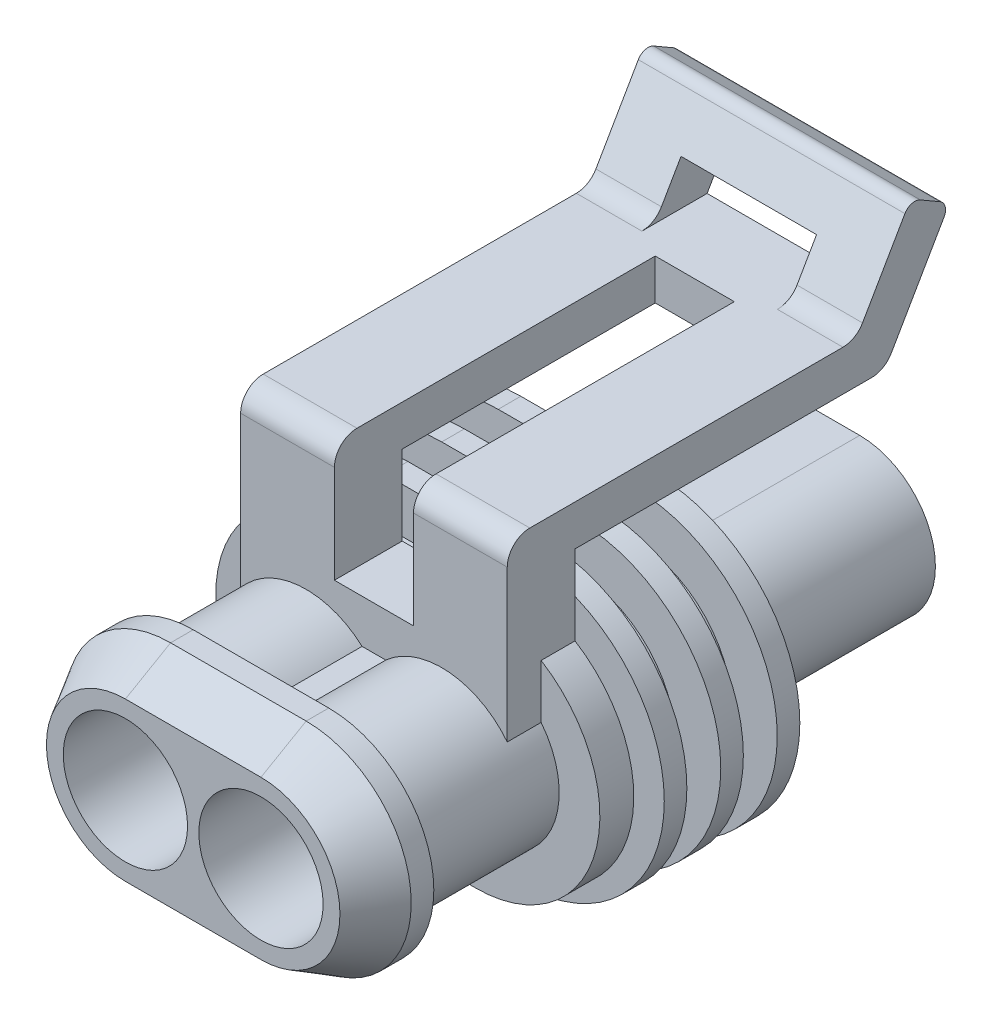
SolidWorks part; units mm, degrees
ref_plane "Plane1" through (0, 0, 0) normal (0, 0, 1) x (1, 0, 0)
ref_plane "Plane2" through (0, 0, 0) normal (0, 1, 0) x (1, 0, 0)
ref_plane "Plane3" through (0, 0, 0) normal (1, 0, 0) x (0, 0, -1)
sketch "Sketch1" plane through (0, 0, 0) normal (0, 0, 1) x (1, 0, 0)
  line L0 (0, 0) -> (3, 0) construction
  line L1 (0, 0) -> (0, 79.049) construction
  line L2 (0.5246, 2.75) -> (-0.5246, 2.75)
  line L3 (0.5246, -2.75) -> (-0.5246, -2.75)
  arc A0 (0.5246, -2.75) -> (0.5246, 2.75) centre (3, 0) ccw
  circle A1 centre (3, 0) radius 2.75
  arc A2 (-0.5246, -2.75) -> (-0.5246, 2.75) centre (-3, 0) cw
  circle A3 centre (-3, 0) radius 2.75
  dimension "D2" = 5.5
  dimension "D3" = 13.4
  dimension "D1" = 6
  dimension "D4" = 5.5
extrude "Extrude1" add sketch "Sketch1" along normal blind 6.5
sketch "Sketch2" plane through (0, 0, 6.5) normal (0, 0, 1) x (1, 0, 0)
  line L0 (0, 0) -> (0, 5.1467) construction
  line L1 (-7.5052, 0) -> (7.5052, 0) construction
  line L2 (3, 4.65) -> (-3, 4.65)
  line L3 (3, -4.65) -> (-3, -4.65)
  arc A2 (3, 4.65) -> (3, -4.65) centre (3, 0) cw
  circle A3 centre (3, 0) radius 2.75 construction
  arc A4 (-3, 4.65) -> (-3, -4.65) centre (-3, 0) ccw
  circle A5 centre (-3, 0) radius 2.75 construction
  circle A6 centre (3, 0) radius 2.75
  circle A7 centre (-3, 0) radius 2.75
  point P10 (0, 4.65)
  point P14 (0, -4.65)
  dimension "D1" = 9.3
extrude "Extrude2" add sketch "Sketch2" along normal blind 3
chamfer "Chamfer1" distance 2 angle 30 4 edges at (-7.65, 0, 9.5) (0, -4.65, 9.5) (0, 4.65, 9.5) (7.65, 0, 9.5)
sketch "Sketch4" plane through (0, 0, 0) normal (0, 0, -1) x (-1, 0, 0)
  line L0 (-8.0826, 0) -> (8.0826, 0) construction
  line L1 (0, 0) -> (0, 7.21) construction
  line L4 (3, 5.5) -> (-3, 5.5)
  line L5 (3, -5.5) -> (-3, -5.5)
  arc A0 (3, 5.5) -> (3, -5.5) centre (3, 0) cw
  circle A1 centre (3, 0) radius 2.75 construction
  arc A2 (-3, 5.5) -> (-3, -5.5) centre (-3, 0) ccw
  circle A3 centre (-3, 0) radius 2.75 construction
  circle A4 centre (3, 0) radius 2.75
  circle A5 centre (-3, 0) radius 2.75
  point P11 (0, 5.5)
  point P15 (0, -5.5)
  dimension "D1" = 11
extrude "Extrude3" add sketch "Sketch4" along normal blind 1.5
sketch "Sketch5" plane through (0, 0, 0) normal (1, 0, 0) x (0, 0, -1)
  line L0 (1.5, 0) -> (1.5, 8.2)
  line L2 (1.5, 8.2) -> (14.6287, 8.2)
  line L3 (15.4947, 8.7) -> (17.833, 12.75)
  line L4 (17.65, 13.433) -> (16.784, 13.933)
  line L5 (16.101, 13.75) -> (14.2246, 10.5)
  line L6 (13.3585, 10) -> (-0.5, 10)
  line L7 (-1.5, 9) -> (-1.5, 0)
  line L8 (1.5, 0) -> (-1.5, 0)
  line L10 (-9.5, 3.4953) -> (-9.5, -3.4953) construction
  line L11 (1.5, -5.5) -> (1.5, 5.5) construction
  arc A0 (16.784, 13.933) -> (16.101, 13.75) centre (16.534, 13.5) ccw
  arc A1 (17.833, 12.75) -> (17.65, 13.433) centre (17.4, 13) ccw
  arc A2 (14.6287, 8.2) -> (15.4947, 8.7) centre (14.6287, 9.2) ccw
  arc A3 (14.2246, 10.5) -> (13.3585, 10) centre (13.3585, 11) cw
  arc A4 (-0.5, 10) -> (-1.5, 9) centre (-0.5, 9) ccw
  dimension "D1" = 0.5
  dimension "D2" = 27.4
  dimension "D8" = 5.8
  dimension "D9" = 1
  dimension "D3" = 60
  dimension "D4" = 2
  dimension "D5" = 1.8
  dimension "D6" = 3
  dimension "D7" = 10
extrude "Extrude4" add sketch "Sketch5" along normal mid plane 11.8
sketch "Sketch6" plane through (0, 0, -1.5) normal (0, 0, -1) x (-1, 0, 0)
  line L0 (0, 0) -> (0, 3.35) construction
  line L1 (-3, 3.35) -> (3, 3.35)
  line L2 (3, -3.35) -> (-3, -3.35)
  arc A0 (3, 3.35) -> (3, -3.35) centre (3, 0) cw
  arc A1 (-3, 3.35) -> (-3, -3.35) centre (-3, 0) ccw
  arc A3 (0.25, 0) -> (5.75, 0) centre (3, 0) ccw construction
  point P10 (0, -3.35)
  dimension "D1" = 12.7
extrude "Extrude5" add sketch "Sketch6" along normal blind 15.5
sketch "Sketch10" plane through (0, 0, 0) normal (1, 0, 0) x (0, 0, -1)
  line L0 (17.4, 12) -> (15.0906, 12)
  line L1 (15.4947, 8.7) -> (17.833, 12.75) construction
  line L2 (16.101, 13.75) -> (14.2246, 10.5) construction
  line L3 (15.0906, 12) -> (13.3585, 10)
  line L4 (13.3585, 10) -> (16.2453, 10)
  line L5 (16.2453, 10) -> (17.4, 12)
  dimension "D1" = 2
extrude "Cut-Extrude1" cut sketch "Sketch10" against normal mid plane 6
sketch "Sketch11" plane through (0, 0, 0) normal (1, 0, 0) x (0, 0, -1)
  line L0 (1.5, 4.6733) -> (-1.5, 4.6733)
  line L1 (-1.5, 9) -> (-1.5, 2.2978) construction
  line L2 (-1.5, 4.6733) -> (-1.5, 10)
  line L3 (-1.5, 10) -> (12.7, 10)
  line L4 (12.7, 10) -> (12.7, 8.2)
  line L5 (1.5, 8.2) -> (14.6287, 8.2) construction
  line L6 (12.7, 8.2) -> (1.5, 8.2)
  line L7 (1.5, 8.2) -> (1.5, 4.6733)
  line L8 (13.3585, 10) -> (-0.5, 10) construction
  dimension "D1" = 14.2
extrude "Cut-Extrude2" cut sketch "Sketch11" against normal mid plane 3.5
sketch "Sketch7" plane through (0, 0, 0) normal (1, 0, 0) x (0, 0, -1)
  line L0 (17, 3.35) -> (1.5, 3.35) construction
  line L1 (8.5, 3.35) -> (1.5, 3.35)
  line L2 (1.5, 3.35) -> (1.5, 4.35)
  line L3 (1.5, 4.35) -> (2, 4.35)
  line L4 (2, 4.35) -> (2, 6.35)
  line L5 (2, 6.35) -> (3, 6.35)
  line L6 (3, 6.35) -> (3, 4.35)
  line L7 (3, 4.35) -> (4.5, 4.35)
  line L8 (4.5, 4.35) -> (4.5, 6.35)
  line L9 (4.5, 6.35) -> (5.5, 6.35)
  line L10 (5.5, 6.35) -> (5.5, 4.35)
  line L11 (5.5, 4.35) -> (7, 4.35)
  line L12 (7, 4.35) -> (7, 6.35)
  line L13 (7, 6.35) -> (8, 6.35)
  line L14 (8, 6.35) -> (8, 4.35)
  line L15 (8, 4.35) -> (8.5, 4.35)
  line L16 (8.5, 4.35) -> (8.5, 3.35)
  dimension "D1" = 7
  dimension "D2" = 1
  dimension "D3" = 3
  dimension "D4" = 1
  dimension "D5" = 1.5
sketch "Sketch8" plane through (0, 0, -1.5) normal (0, 0, -1) x (-1, 0, 0)
  line L0 (3, 3.35) -> (-3, 3.35) construction
  line L1 (3, 3.35) -> (-3, 3.35)
  line L2 (-3, -3.35) -> (3, -3.35) construction
  line L3 (-3, -3.35) -> (3, -3.35)
  arc A0 (3, -3.35) -> (3, 3.35) centre (3, 0) ccw construction
  arc A1 (3, -3.35) -> (3, 3.35) centre (3, 0) ccw
  arc A2 (-3, 3.35) -> (-3, -3.35) centre (-3, 0) ccw construction
  arc A3 (-3, 3.35) -> (-3, -3.35) centre (-3, 0) ccw
sweep "Bælg" add profiles "Sketch7" path "Sketch8"
